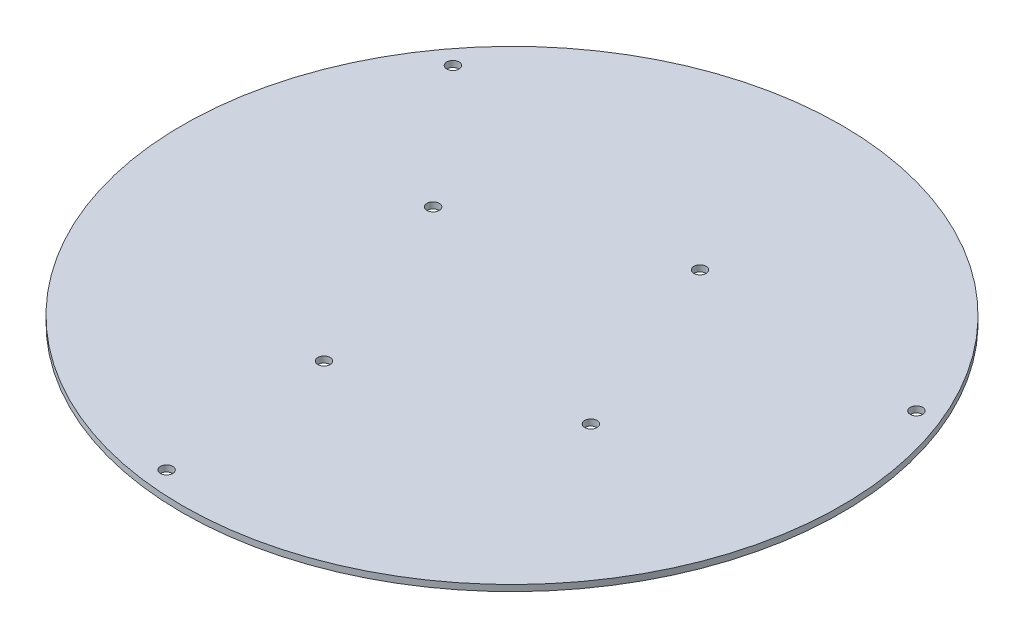
SolidWorks part; units mm, degrees
material "Aleación 1060"
ref_plane "Front Plane" through (0, 0, 0) normal (0, 0, 1) x (1, 0, 0)
ref_plane "Top Plane" through (0, 0, 0) normal (0, 1, 0) x (1, 0, 0)
ref_plane "Right Plane" through (0, 0, 0) normal (1, 0, 0) x (0, 0, -1)
sketch "Croquis1" plane through (0, 0, 0) normal (0, 1, 0) x (1, 0, 0)
  line L0 (0, 0) -> (138.3138, 58.0457) construction
  line L1 (138.3138, 58.0457) -> (-18.8878, -148.8061) construction
  line L2 (-18.8878, -148.8061) -> (-119.4259, 90.7604) construction
  line L3 (-119.4259, 90.7604) -> (138.3138, 58.0457) construction
  line L4 (-64.7949, 26.4882) -> (26.4882, 64.7949) construction
  line L5 (26.4882, 64.7949) -> (64.7949, -26.4882) construction
  line L6 (64.7949, -26.4882) -> (-26.4882, -64.7949) construction
  line L7 (-26.4882, -64.7949) -> (-64.7949, 26.4882) construction
  line L8 (0, 0) -> (26.4882, 64.7949) construction
  circle A0 centre (0, 0) radius 160
  circle A3 centre (138.3138, 58.0457) radius 3
  circle A4 centre (-18.8878, -148.8061) radius 3
  circle A5 centre (-64.7949, 26.4882) radius 3
  circle A6 centre (26.4882, 64.7949) radius 3
  circle A7 centre (64.7949, -26.4882) radius 3
  circle A8 centre (-26.4882, -64.7949) radius 3
  circle A9 centre (-119.4259, 90.7604) radius 3
  dimension "D1" = 70
extrude "Saliente-Extruir2" add sketch "Croquis1" along normal blind 3
